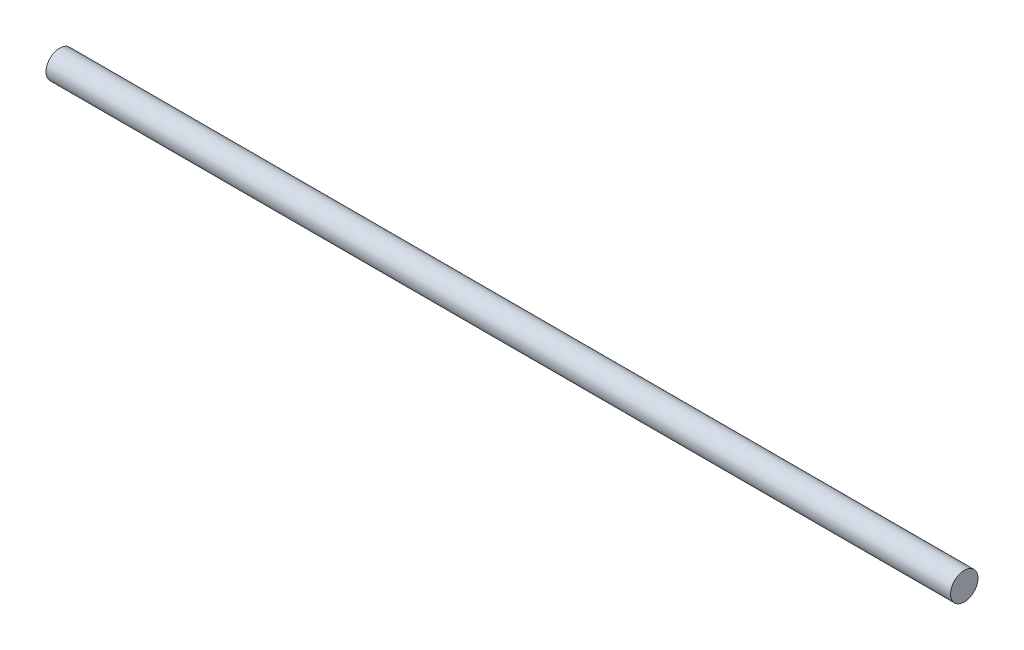
SolidWorks part; units mm, degrees
material "1023 Carbon Steel Sheet (SS)"
ref_plane "Front Plane" through (0, 0, 0) normal (0, 0, 1) x (1, 0, 0)
ref_plane "Top Plane" through (0, 0, 0) normal (0, 1, 0) x (1, 0, 0)
ref_plane "Right Plane" through (0, 0, 0) normal (1, 0, 0) x (0, 0, -1)
sketch "Sketch1" plane through (0, 0, 0) normal (1, 0, 0) x (0, 0, -1)
  circle A0 centre (0, 0) radius 10.795
  dimension "D1" = 21.59
extrude "Boss-Extrude1" add sketch "Sketch1" along normal mid plane 711.2
